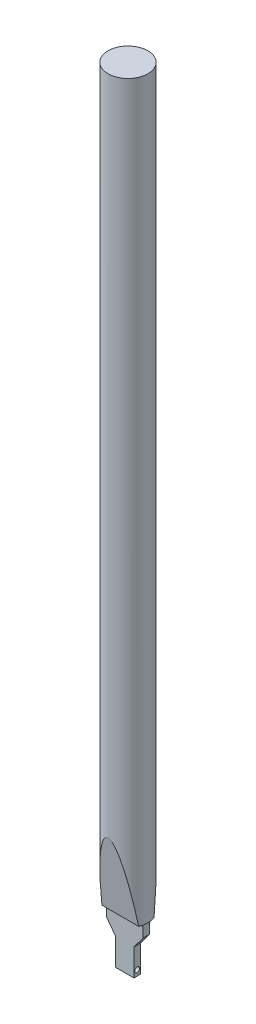
SolidWorks part; units mm, degrees
ref_plane "Front Plane" through (0, 0, 0) normal (0, 0, 1) x (1, 0, 0)
ref_plane "Top Plane" through (0, 0, 0) normal (0, 1, 0) x (1, 0, 0)
ref_plane "Right Plane" through (0, 0, 0) normal (1, 0, 0) x (0, 0, -1)
sketch "Sketch1" plane through (0, 0, 0) normal (0, 1, 0) x (1, 0, 0)
  line L1 (-1.5, 0.525) -> (1.5, 0.525)
  line L2 (-1.5, 0.525) -> (-1.5, -0.525)
  line L3 (-1.5, -0.525) -> (1.5, -0.525)
  line L4 (1.5, 0.525) -> (1.5, -0.525)
  line L5 (-1.5, 0.525) -> (1.5, -0.525) construction
  line L6 (-1.5, -0.525) -> (1.5, 0.525) construction
  point P0 (0, 0)
  dimension "D1" = 1.05
  dimension "D2" = 3
extrude "Boss-Extrude1" add sketch "Sketch1" along normal blind 2.4
sketch "Sketch2" plane through (1.5, 0, 0) normal (1, 0, 0) x (0, 0, -1)
  line L0 (-0.525, 2.4) -> (0.525, 2.4) construction
  circle A0 centre (0, 0.9) radius 0.4
  dimension "D3" = 0.8
  dimension "D1" = 0
  dimension "D2" = 1.5
extrude "Cut-Extrude1" cut sketch "Sketch2" against normal up to surface (3 mm away) up to face at (-1.5, 1.2, 0)
sketch "Sketch3" plane through (0, 0, 0.525) normal (0, 0, 1) x (1, 0, 0)
  line L0 (-1.5, 2.4) -> (1.5, 2.4)
  line L1 (-1.5, 2.4) -> (-1.5, 4.4)
  line L2 (1.5, 2.4) -> (1.5, 4.4)
  line L3 (-1.5, 4.4) -> (1.5, 4.4)
  line L4 (-3, 6.4) -> (-1.5, 4.4)
  line L5 (-3, 8.4) -> (3, 8.4)
  line L6 (-3, 8.4) -> (-3, 6.4)
  line L7 (-3, 6.4) -> (3, 6.4)
  line L8 (3, 8.4) -> (3, 6.4)
  line L9 (-3, 8.4) -> (3, 6.4) construction
  line L10 (-3, 6.4) -> (3, 8.4) construction
  line L11 (3, 6.4) -> (1.5, 4.4)
  point P0 (0, 7.4)
  line M8 (1.5, 2.4) -> (-1.5, 2.4)
  dimension "D1" = 2
  dimension "D2" = 6
  dimension "D3" = 0
  dimension "D4" = 2
  dimension "D5" = 2
extrude "Boss-Extrude2" add sketch "Sketch3" against normal up to surface (1.05 mm away) contours L8 L5 L6 L7 | L11 L7 L4 L3 | L3 L1 L2 M8 up to face at (0, 1.2, -0.525)
sketch "Sketch4" plane through (0, 0, 0) normal (0, -1, 0) x (1, 0, 0)
  circle A0 centre (0, 0) radius 0.25
  dimension "D1" = 0.5
extrude "Cut-Extrude2" cut sketch "Sketch4" against normal up to surface (0.5878 mm away)
sketch "Sketch5" plane through (0, 8.4, 0) normal (0, 1, 0) x (1, 0, 0)
  circle A0 centre (0, 0) radius 3.25
  dimension "D1" = 6.5
  dimension "D2" = 0
  dimension "D3" = 0
extrude "Boss-Extrude3" add sketch "Sketch5" along normal blind 120
fillet "Fillet2" radius 0.5 2 edges at (0, 8.4, -0.525) (0, 8.4, 0.525)
sketch "Sketch6" plane through (0, 0, 0) normal (1, 0, 0) x (0, 0, -1)
  line L0 (-3.25, 8.4) -> (-3.25, 20.4)
  line L1 (-3.25, 128.4) -> (-3.25, 8.4) construction
  line L2 (-3.25, 20.4) -> (-1.25, 8.4)
  line L3 (-3.25, 8.4) -> (3.25, 8.4) construction
  line L4 (-1.25, 8.4) -> (-3.25, 8.4)
  line L5 (3.25, 8.4) -> (3.25, 20.4)
  line L6 (3.25, 8.4) -> (3.25, 128.4) construction
  line L7 (3.25, 20.4) -> (1.25, 8.4)
  line L8 (1.25, 8.4) -> (3.25, 8.4)
  dimension "D1" = 12
  dimension "D2" = 2
  dimension "D3" = 2
  dimension "D4" = 0
extrude "Cut-Extrude3" cut sketch "Sketch6" against normal mid plane 6.5
